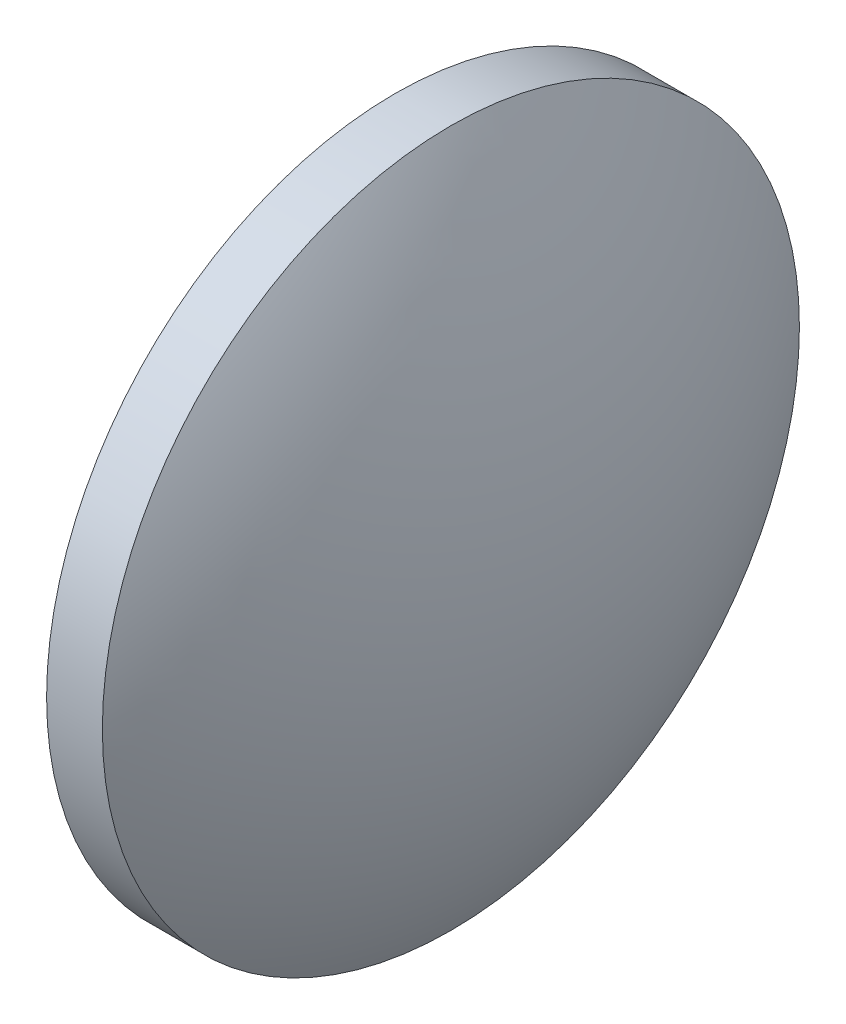
SolidWorks part; units mm, degrees
ref_plane "前视基准面" through (0, 0, 0) normal (0, 0, 1) x (1, 0, 0)
ref_plane "上视基准面" through (0, 0, 0) normal (0, 1, 0) x (1, 0, 0)
ref_plane "右视基准面" through (0, 0, 0) normal (1, 0, 0) x (0, 0, -1)
sketch "草图1" plane through (0, 0, 0) normal (0, 0, 1) x (1, 0, 0)
  line L0 (84.0966, 60.3505) -> (86.0966, 60.3505)
  line L1 (86.0966, 60.3505) -> (86.0966, 35.3505)
  line L2 (86.0966, 35.3505) -> (84.0966, 35.3505)
  line L3 (84.0966, 35.3505) -> (84.0966, 60.3505)
  line L4 (76.6262, 47.8505) -> (91.2235, 47.8505) construction
  arc A0 (84.0966, 60.3505) -> (84.0966, 35.3505) centre (104.8064, 47.8505) ccw
  arc A1 (86.0966, 35.3505) -> (86.0966, 60.3505) centre (65.3869, 47.8505) ccw
  dimension "D1" = 2
  dimension "D2" = 25
revolve "旋转1" add sketch "草图1" angle 360 about L4
